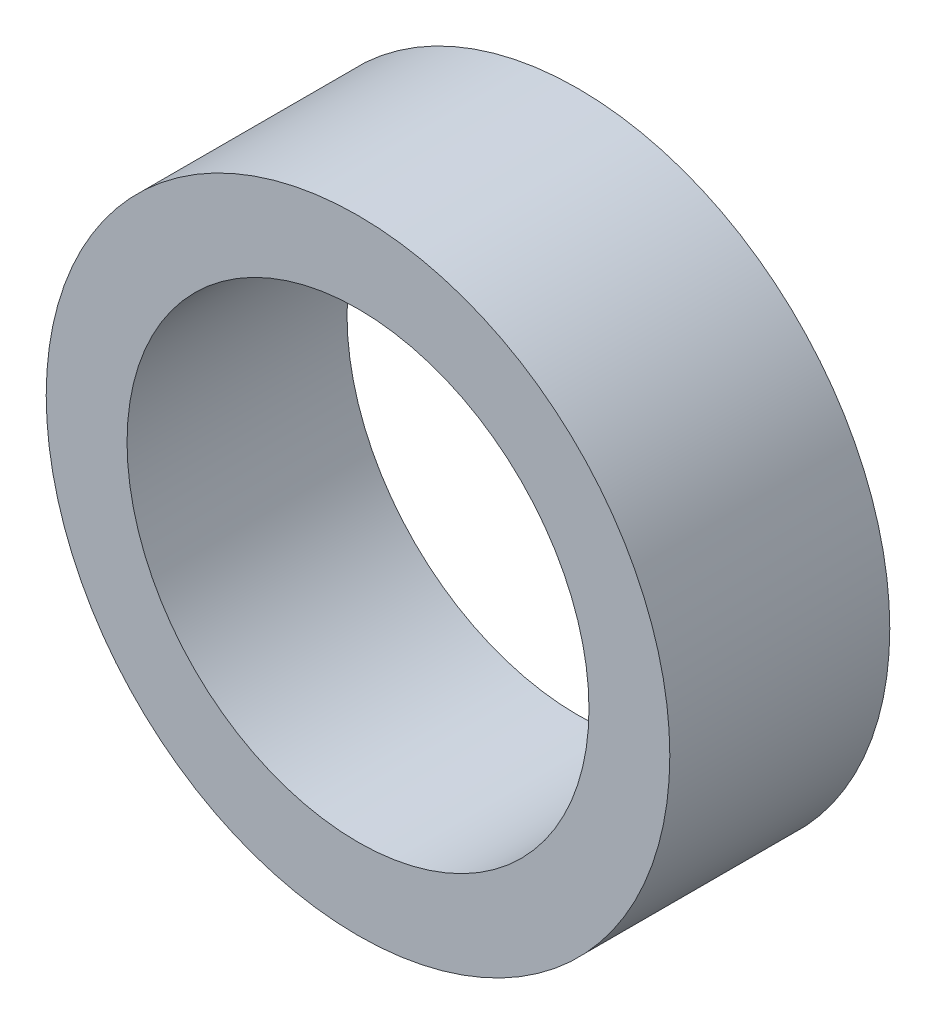
SolidWorks part; units mm, degrees
ref_plane "Front Plane" through (0, 0, 0) normal (0, 0, 1) x (1, 0, 0)
ref_plane "Top Plane" through (0, 0, 0) normal (0, 1, 0) x (1, 0, 0)
ref_plane "Right Plane" through (0, 0, 0) normal (1, 0, 0) x (0, 0, -1)
sketch "Sketch1" plane through (0, 0, 0) normal (0, 0, 1) x (1, 0, 0)
  circle A0 centre (0, 0) radius 28.35
  circle A1 centre (0, 0) radius 21
  dimension "D1" = 42
extrude "Boss-Extrude1" add sketch "Sketch1" along normal blind 20
